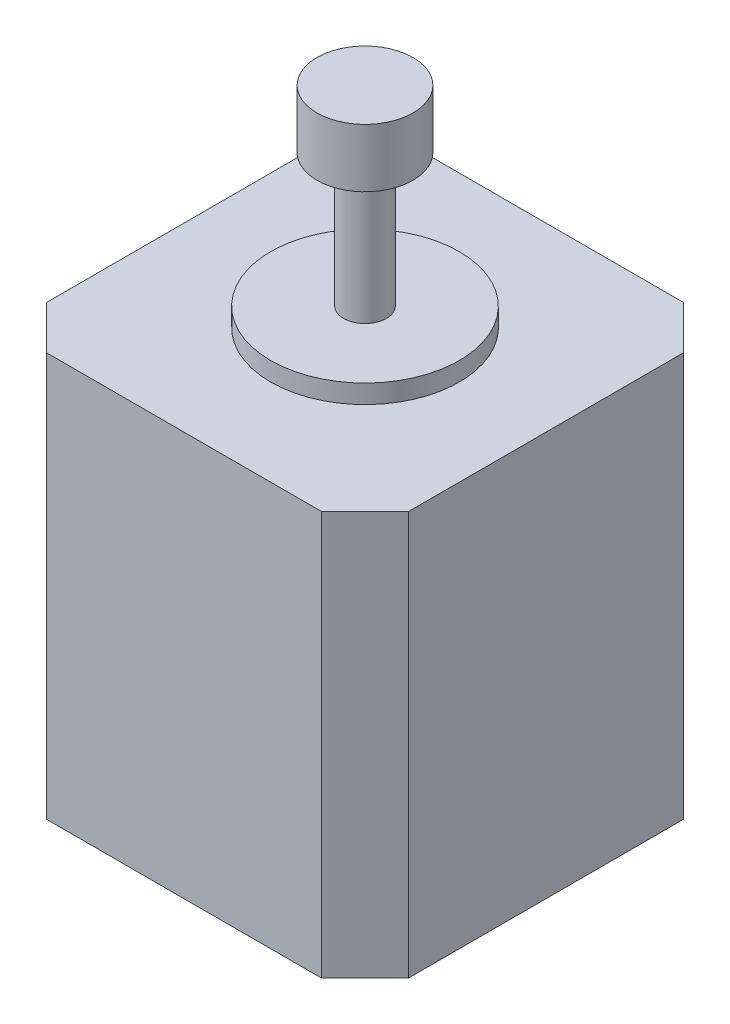
SolidWorks part; units mm, degrees
ref_plane "Front Plane" through (0, 0, 0) normal (0, 0, 1) x (1, 0, 0)
ref_plane "Top Plane" through (0, 0, 0) normal (0, 1, 0) x (1, 0, 0)
ref_plane "Right Plane" through (0, 0, 0) normal (1, 0, 0) x (0, 0, -1)
sketch "Sketch1" plane through (0, 0, 0) normal (0, 1, 0) x (1, 0, 0)
  line L1 (0, 0) -> (42.1386, 0)
  line L2 (0, 0) -> (0, 42.1386)
  line L3 (0, 42.1386) -> (42.1386, 42.1386)
  line L4 (42.1386, 0) -> (42.1386, 42.1386)
extrude "Boss-Extrude1" add sketch "Sketch1" along normal blind 47.0281
sketch "Sketch2" plane through (0, 47.0281, 0) normal (0, 1, 0) x (1, 0, 0)
  line L0 (0, 42.1386) -> (42.1386, 0) construction
  line L1 (42.1386, 0) -> (0, 0) construction
  line L2 (0, 0) -> (42.1386, 42.1386) construction
  circle A0 centre (21.0693, 21.0693) radius 10.9792
extrude "Boss-Extrude2" add sketch "Sketch2" along normal blind 2.1717
sketch "Sketch3" plane through (0, 49.1998, 0) normal (0, 1, 0) x (1, 0, 0)
  circle A0 centre (21.0693, 21.0693) radius 2.4956
extrude "Boss-Extrude3" add sketch "Sketch3" along normal blind 15.4686
chamfer "Chamfer1" distance 5.08 angle 45 1 edges at (42.1386, 23.514, -42.1386)
chamfer "Chamfer2" distance 5.08 angle 45 1 edges at (42.1386, 23.514, 0)
chamfer "Chamfer3" distance 5.08 angle 45 1 edges at (0, 23.514, 0)
chamfer "Chamfer4" distance 5.08 angle 45 1 edges at (0, 23.514, -42.1386)
sketch "Sketch4" plane through (0, 0, 0) normal (0, -1, 0) x (1, 0, 0)
  line L0 (2.54, -39.5986) -> (39.5986, -2.54) construction
  line L1 (5.08, -42.1386) -> (0, -37.0586) construction
  line L2 (37.0586, 0) -> (42.1386, -5.08) construction
sketch "Sketch5" plane through (0, 64.6684, 0) normal (0, 1, 0) x (1, 0, 0)
  line L0 (2.54, 39.5986) -> (39.5986, 2.54) construction
  circle A0 centre (21.0693, 21.0693) radius 5.588
extrude "Boss-Extrude4" add sketch "Sketch5" along normal blind 6.7945
